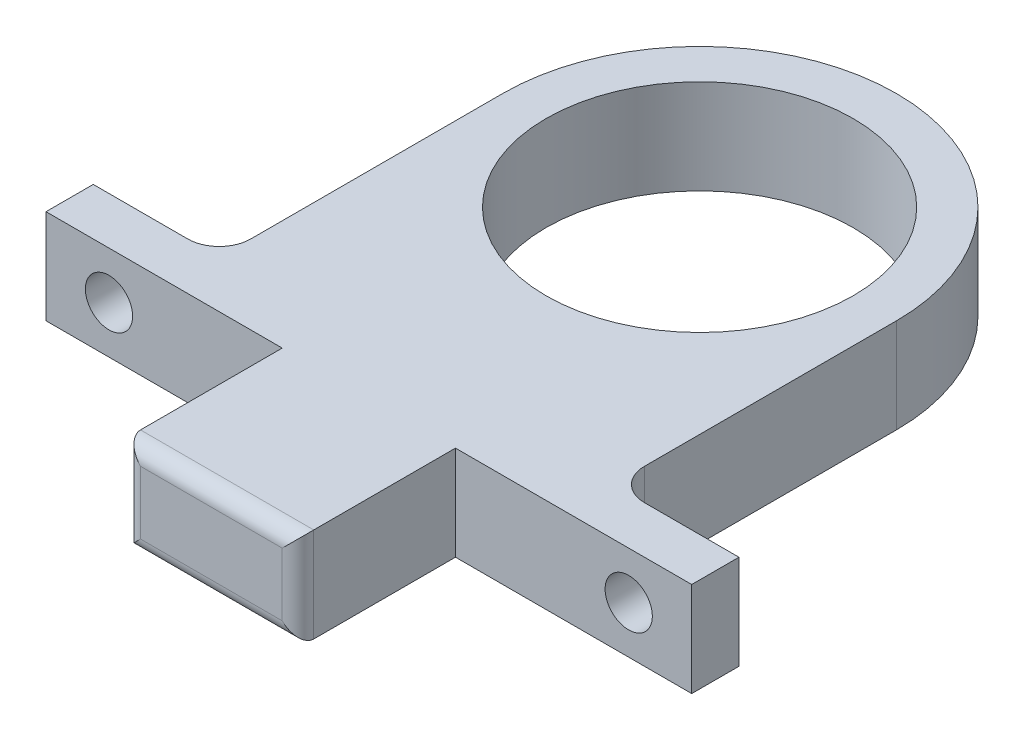
SolidWorks part; units mm, degrees
ref_plane "Alzado" through (0, 0, 0) normal (0, 0, 1) x (1, 0, 0)
ref_plane "Planta" through (0, 0, 0) normal (0, 1, 0) x (1, 0, 0)
ref_plane "Vista lateral" through (0, 0, 0) normal (1, 0, 0) x (0, 0, -1)
sketch "Croquis1" plane through (0, 0, 0) normal (0, 1, 0) x (1, 0, 0)
  line L0 (-12.5, 0) -> (12.5, 0) construction
  line L1 (-12.5, 0) -> (-12.5, -16)
  line L2 (-12.5, -21) -> (12.5, -21)
  line L3 (12.5, -16) -> (12.5, 0)
  line L4 (-20.5, -18) -> (20.5, -18) construction
  line L6 (-20.5, -18) -> (-14.5, -18)
  line L7 (-20.5, -18) -> (-20.5, -21)
  line L8 (-20.5, -21) -> (-12.5, -21)
  line L9 (-12.5, -14) -> (-12.5, -21)
  line L10 (20.5, -18) -> (14.5, -18)
  line L11 (20.5, -18) -> (20.5, -21)
  line L12 (20.5, -21) -> (12.5, -21)
  line L13 (12.5, -14) -> (12.5, -21)
  line L14 (-5.5, -21) -> (5.5, -21)
  line L15 (-5.5, -21) -> (-5.5, -31)
  line L16 (-5.5, -31) -> (5.5, -31)
  line L17 (5.5, -21) -> (5.5, -31)
  circle A0 centre (0, 0) radius 12.5
  circle A1 centre (0, 0) radius 9.75
  arc A2 (14.5, -18) -> (12.5, -16) centre (14.5, -16) cw
  arc A3 (-14.5, -18) -> (-12.5, -16) centre (-14.5, -16) ccw
  dimension "D1" = 25
  dimension "D2" = 19.5
  dimension "D6" = 2
  dimension "D3" = 21
  dimension "D4" = 3
  dimension "D5" = 8
  dimension "D7" = 8
  dimension "D8" = 25
  dimension "D9" = 12.5
  dimension "D10" = 11
  dimension "D11" = 10
  dimension "D12" = 5.5
extrude "Saliente-Extruir1" add sketch "Croquis1" along normal blind 6
sketch "Croquis2" plane through (0, 0, 21) normal (0, 0, 1) x (1, 0, 0)
  line L0 (-20.5, 3) -> (20.5, 3) construction
  line L1 (-20.5, 6) -> (-20.5, 0) construction
  line L2 (20.5, 6) -> (20.5, 0) construction
  circle A0 centre (-16.5, 3) radius 1.5
  circle A1 centre (16.5, 3) radius 1.5
  dimension "D3" = 3
  dimension "D4" = 3
  dimension "D1" = 4
  dimension "D2" = 4
extrude "Cortar-Extruir1" cut sketch "Croquis2" against normal blind 6
sketch "Croquis3" plane through (0, 0, 18) normal (0, 0, -1) x (-1, 0, 0)
  circle A0 centre (-16.5, 3) radius 3
  circle A1 centre (16.5, 3) radius 3
  dimension "D1" = 6
  dimension "D2" = 6
extrude "Cortar-Extruir2" cut sketch "Croquis3" along normal blind 6
fillet "Redondeo1" radius 1 4 edges at (5.5, 3, 31) (-5.5, 3, 31) (0, 0, 31) (0, 6, 31)
